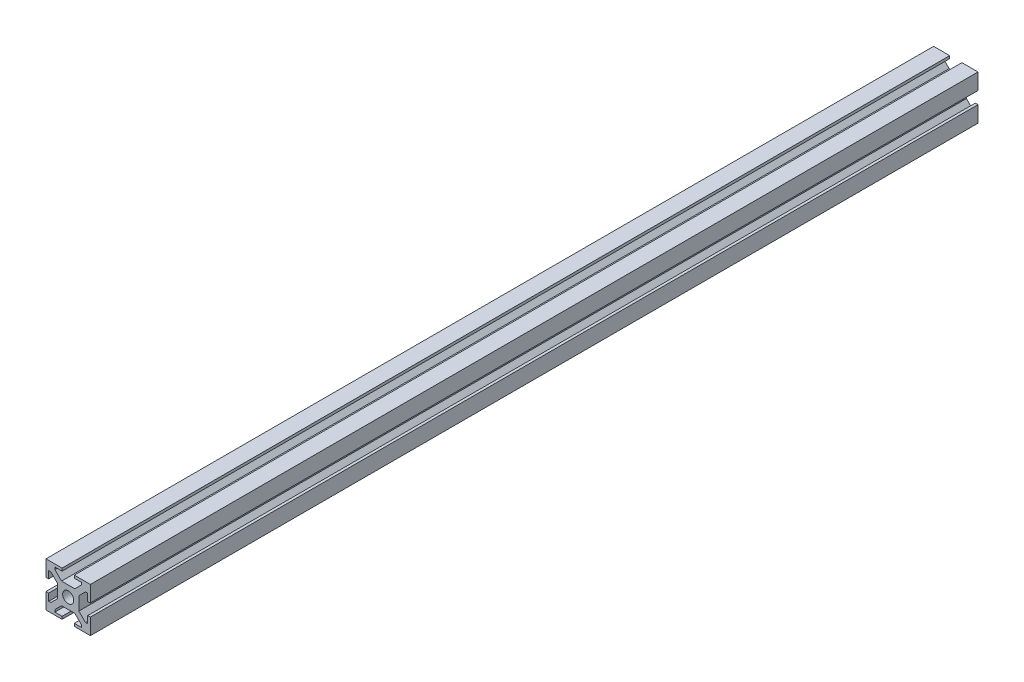
SolidWorks part; units mm, degrees
ref_plane "Plan de face" through (0, 0, 0) normal (0, 0, 1) x (1, 0, 0)
ref_plane "Plan de dessus" through (0, 0, 0) normal (0, 1, 0) x (1, 0, 0)
ref_plane "Plan de droite" through (0, 0, 0) normal (1, 0, 0) x (0, 0, -1)
sketch "Esquisse1" plane through (0, 0, 0) normal (0, 0, 1) x (1, 0, 0)
  line L1 (-22.5051, 0.0904) -> (-2.5051, 0.0904)
  line L2 (-22.5051, 0.0904) -> (-22.5051, -19.9096)
  line L3 (-22.5051, -19.9096) -> (-2.5051, -19.9096)
  line L4 (-2.5051, 0.0904) -> (-2.5051, -19.9096)
  dimension "D1" = 20
  dimension "D2" = 20
extrude "Boss.-Extru.1" add sketch "Esquisse1" along normal blind 400
sketch "Esquisse2" plane through (0, 0, 400) normal (0, 0, 1) x (1, 0, 0)
  line L0 (-22.5051, 0.0904) -> (-22.5051, -19.9096) construction
  line L1 (-22.5051, -7.1596) -> (-21.3051, -7.1596)
  line L2 (-22.5051, -7.1596) -> (-22.5051, -12.6596)
  line L3 (-22.5051, -12.6596) -> (-21.3051, -12.6596)
  line L4 (-21.3051, -7.1596) -> (-21.3051, -12.6596)
  line L5 (-2.5051, 0.0904) -> (-22.5051, 0.0904) construction
  line L6 (-15.2551, 0.0904) -> (-9.7551, 0.0904)
  line L7 (-15.2551, 0.0904) -> (-15.2551, -1.1096)
  line L8 (-15.2551, -1.1096) -> (-9.7551, -1.1096)
  line L9 (-9.7551, 0.0904) -> (-9.7551, -1.1096)
  line L10 (-2.5051, -19.9096) -> (-2.5051, 0.0904) construction
  line L11 (-2.5051, -7.1596) -> (-3.7051, -7.1596)
  line L12 (-2.5051, -7.1596) -> (-2.5051, -12.6596)
  line L13 (-2.5051, -12.6596) -> (-3.7051, -12.6596)
  line L14 (-3.7051, -7.1596) -> (-3.7051, -12.6596)
  line L15 (-22.5051, -19.9096) -> (-2.5051, -19.9096) construction
  line L16 (-15.2551, -19.9096) -> (-9.7551, -19.9096)
  line L17 (-15.2551, -19.9096) -> (-15.2551, -18.7096)
  line L18 (-15.2551, -18.7096) -> (-9.7551, -18.7096)
  line L19 (-9.7551, -19.9096) -> (-9.7551, -18.7096)
  dimension "D1" = 1.2
  dimension "D2" = 1.2
  dimension "D3" = 1.2
  dimension "D4" = 1.2
  dimension "D5" = 5.5
  dimension "D6" = 5.5
  dimension "D7" = 5.5
  dimension "D8" = 5.5
  dimension "D9" = 7.25
  dimension "D10" = 7.25
  dimension "D11" = 7.25
  dimension "D12" = 7.25
extrude "Enlèv. mat.-Extru.1" cut sketch "Esquisse2" against normal through all
sketch "Esquisse3" plane through (0, 0, 400) normal (0, 0, 1) x (1, 0, 0)
  line L0 (-15.2551, 0.0904) -> (-22.5051, 0.0904) construction
  line L1 (-21.3051, -15.9096) -> (-20.3051, -15.9096)
  line L2 (-21.3051, -15.9096) -> (-21.3051, -3.9096)
  line L3 (-21.3051, -3.9096) -> (-20.3051, -3.9096)
  line L4 (-17.3051, -12.9096) -> (-17.3051, -6.9096)
  line L5 (-18.5051, -1.1096) -> (-6.5051, -1.1096)
  line L6 (-18.5051, -1.1096) -> (-18.5051, -2.1096)
  line L7 (-15.5051, -5.1096) -> (-9.5051, -5.1096)
  line L8 (-6.5051, -1.1096) -> (-6.5051, -2.1096)
  line L9 (-3.7051, -3.9096) -> (-4.7051, -3.9096)
  line L10 (-3.7051, -3.9096) -> (-3.7051, -15.9096)
  line L11 (-3.7051, -15.9096) -> (-4.7051, -15.9096)
  line L12 (-7.7051, -6.9096) -> (-7.7051, -12.9096)
  line L13 (-6.5051, -18.7096) -> (-18.5051, -18.7096)
  line L14 (-6.5051, -18.7096) -> (-6.5051, -17.7096)
  line L15 (-9.5051, -14.7096) -> (-15.5051, -14.7096)
  line L16 (-18.5051, -18.7096) -> (-18.5051, -17.7096)
  line L17 (-2.5051, -7.1596) -> (-2.5051, 0.0904) construction
  line L18 (-15.2551, -1.1096) -> (-9.7551, -1.1096) construction
  line L19 (-3.7051, -7.1596) -> (-3.7051, -12.6596) construction
  line L20 (-9.7551, -19.9096) -> (-2.5051, -19.9096) construction
  line L21 (-22.5051, -12.6596) -> (-22.5051, -19.9096) construction
  line L22 (-22.5051, -19.9096) -> (-15.2551, -19.9096) construction
  line L23 (-15.5051, -14.7096) -> (-18.5051, -17.7096)
  line L24 (-20.3051, -15.9096) -> (-17.3051, -12.9096)
  line L25 (-6.5051, -17.7096) -> (-9.5051, -14.7096)
  line L26 (-4.7051, -15.9096) -> (-7.7051, -12.9096)
  line L27 (-4.7051, -3.9096) -> (-7.7051, -6.9096)
  line L28 (-9.5051, -5.1096) -> (-6.5051, -2.1096)
  line L29 (-18.5051, -2.1096) -> (-15.5051, -5.1096)
  line L30 (-20.3051, -3.9096) -> (-17.3051, -6.9096)
  point P1 (-17.3051, -3.9096)
  point P3 (-17.3051, -15.9096)
  point P5 (-6.5051, -5.1096)
  point P6 (-18.5051, -5.1096)
  point P9 (-7.7051, -15.9096)
  point P11 (-7.7051, -3.9096)
  point P13 (-18.5051, -14.7096)
  point P14 (-6.5051, -14.7096)
  point P24 (-6.1301, -19.9096)
  dimension "D1" = 4
  dimension "D2" = 4
  dimension "D3" = 4
  dimension "D4" = 4
  dimension "D5" = 12
  dimension "D6" = 4
  dimension "D7" = 12
  dimension "D8" = 4
  dimension "D9" = 0
  dimension "D10" = 0
  dimension "D11" = 4
  dimension "D12" = 12
  dimension "D13" = 12
  dimension "D14" = 4
  dimension "D15" = 1.2
  dimension "D16" = 1.2
  dimension "D17" = 3
  dimension "D18" = 3
  dimension "D19" = 3
  dimension "D20" = 3
  dimension "D21" = 3
  dimension "D22" = 3
  dimension "D23" = 3
  dimension "D24" = 3
  dimension "D25" = 3
  dimension "D26" = 3
  dimension "D27" = 3
  dimension "D28" = 3
  dimension "D29" = 3
  dimension "D30" = 3
  dimension "D31" = 3
  dimension "D32" = 3
extrude "Enlèv. mat.-Extru.2" cut sketch "Esquisse3" against normal through all
sketch "Esquisse4" plane through (0, 0, 400) normal (0, 0, 1) x (1, 0, 0)
  line L0 (-15.5051, -5.1096) -> (-9.5051, -5.1096) construction
  line L2 (-17.3051, -12.9096) -> (-17.3051, -6.9096) construction
  circle A0 centre (-12.5051, -9.9096) radius 2.5
  dimension "D1" = 5
  dimension "D2" = 4.8
  dimension "D3" = 4.8
extrude "Enlèv. mat.-Extru.3" cut sketch "Esquisse4" against normal through all
